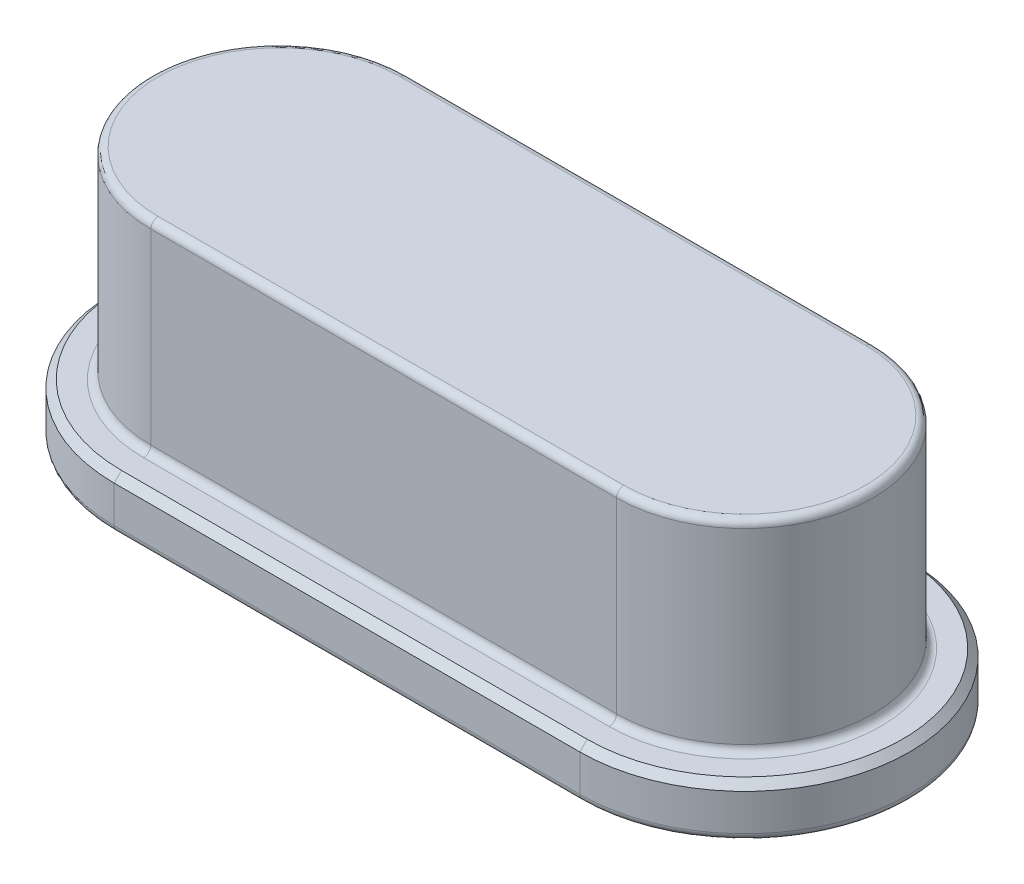
SolidWorks part; units mm, degrees
ref_plane "Plan de face" through (0, 0, 0) normal (0, 0, 1) x (1, 0, 0)
ref_plane "Plan de dessus" through (0, 0, 0) normal (0, 1, 0) x (1, 0, 0)
ref_plane "Plan de droite" through (0, 0, 0) normal (1, 0, 0) x (0, 0, -1)
sketch "Esquisse1" plane through (0, 0, 0) normal (0, 1, 0) x (1, 0, 0)
  line L0 (0, 0) -> (6.35, 0) construction
  line L1 (0, 2.25) -> (6.35, 2.25)
  line L2 (0, -2.25) -> (6.35, -2.25)
  line L3 (-2.25, 0) -> (-2.25, 5.2002) construction
  line L4 (8.6, 0) -> (8.6, 4.7369) construction
  arc A0 (0, 2.25) -> (0, -2.25) centre (0, 0) ccw
  arc A1 (6.35, -2.25) -> (6.35, 2.25) centre (6.35, 0) ccw
  point P3 (3.175, 0)
  dimension "D2" = 10.85
  dimension "D1" = 4.5
extrude "Boss.-Extru.1" add sketch "Esquisse1" along normal blind 0.7
sketch "Esquisse2" plane through (0, 0.7, 0) normal (0, 1, 0) x (1, 0, 0)
  line L0 (-2.25, 0) -> (8.6, 0) construction
  line L1 (0, 0) -> (6.35, 0) construction
  line L2 (0, 1.75) -> (6.35, 1.75)
  line L3 (0, -1.75) -> (6.35, -1.75)
  line L4 (-1.75, 0) -> (-1.75, 0.9011) construction
  line L5 (8.1, 0) -> (8.1, 1.1386) construction
  line L6 (3.175, 2.25) -> (3.175, -2.25) construction
  line L7 (6.35, 2.25) -> (0, 2.25) construction
  line L8 (0, -2.25) -> (6.35, -2.25) construction
  line L9 (3.175, 1.75) -> (3.175, -1.75) construction
  arc A0 (0, 2.25) -> (0, -2.25) centre (0, 0) ccw construction
  arc A1 (6.35, -2.25) -> (6.35, 2.25) centre (6.35, 0) ccw construction
  arc A2 (0, 1.75) -> (0, -1.75) centre (0, 0) ccw
  arc A3 (6.35, -1.75) -> (6.35, 1.75) centre (6.35, 0) ccw
  point P10 (3.175, 0)
  dimension "D1" = 9.85
  dimension "D2" = 3.5
extrude "Boss.-Extru.2" add sketch "Esquisse2" along normal blind 2.75
fillet "Congé1" radius 0.1 4 edges at (3.175, 0.7, -1.75) (8.1, 0.7, 0) (3.175, 0.7, 1.75) (-1.75, 0.7, 0)
fillet "Congé2" radius 0.1 4 edges at (-1.75, 3.45, 0) (3.175, 3.45, 1.75) (3.175, 3.45, -1.75) (8.1, 3.45, 0)
fillet "Congé3" radius 0.1 4 edges at (3.175, 0, -2.25) (-2.25, 0, 0) (3.175, 0, 2.25) (8.6, 0, 0)
chamfer "Chanfrein1" distance 0.1 angle 45 4 edges at (3.175, 0.7, -2.25) (8.6, 0.7, 0) (3.175, 0.7, 2.25) (-2.25, 0.7, 0)
